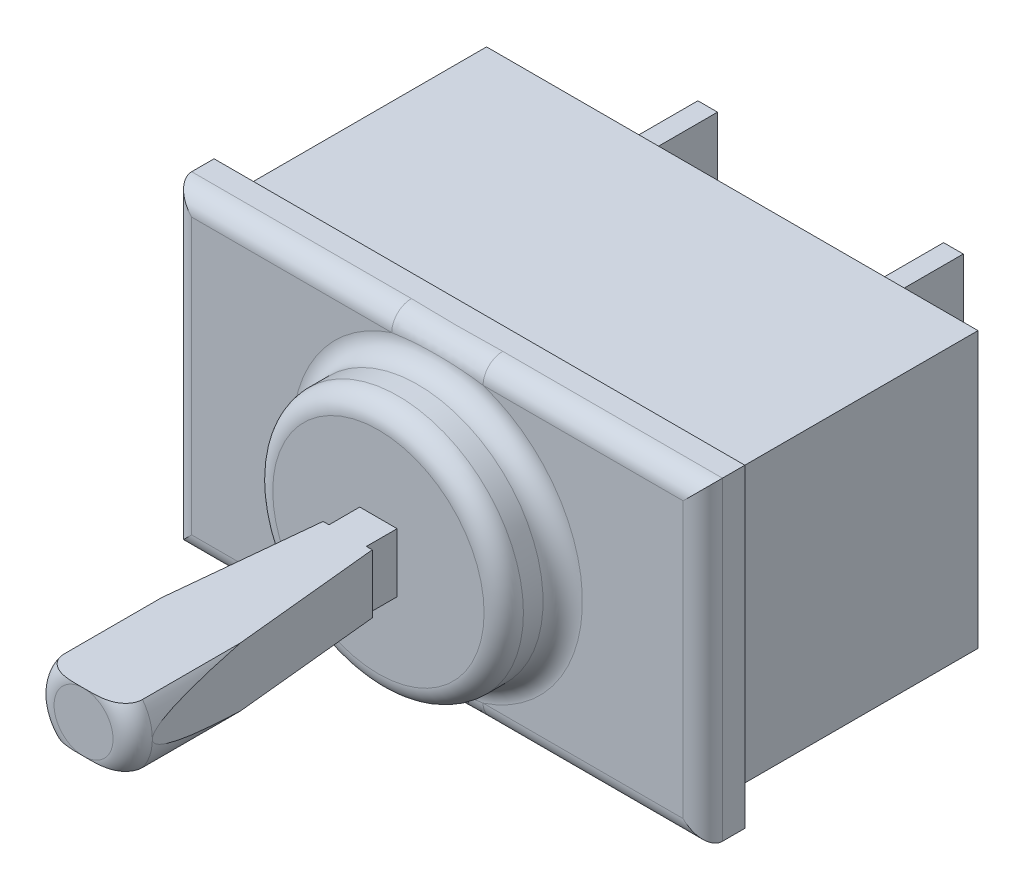
SolidWorks part; units mm, degrees
ref_plane "Front Plane" through (0, 0, 0) normal (0, 0, 1) x (1, 0, 0)
ref_plane "Top Plane" through (0, 0, 0) normal (0, 1, 0) x (1, 0, 0)
ref_plane "Right Plane" through (0, 0, 0) normal (1, 0, 0) x (0, 0, -1)
sketch "Esquisse1" plane through (0, 0, 0) normal (0, 1, 0) x (1, 0, 0)
  line L1 (-13.5, -7.5) -> (13.5, -7.5)
  line L2 (-13.5, -7.5) -> (-13.5, 7.5)
  line L3 (-13.5, 7.5) -> (13.5, 7.5)
  line L4 (13.5, -7.5) -> (13.5, 7.5)
  line L5 (-13.5, -7.5) -> (13.5, 7.5) construction
  line L6 (-13.5, 7.5) -> (13.5, -7.5) construction
  point P0 (0, 0)
  dimension "D1" = 27
  dimension "D2" = 15
extrude "Boss.-Extru.1" add sketch "Esquisse1" along normal blind 16
sketch "Esquisse2" plane through (0, 0, 0) normal (0, -1, 0) x (1, 0, 0)
  line L0 (-13.5, -7.5) -> (-13.5, 7.5) construction
  line L1 (-13.5, 5.3607) -> (13.5, 5.3607)
  line L2 (-13.5, 5.3607) -> (-13.5, -7.5)
  line L3 (-13.5, -7.5) -> (13.5, -7.5)
  line L4 (13.5, 5.3607) -> (13.5, -7.5)
  line L6 (-12.5, 5.3607) -> (12.5, 5.3607)
  line L7 (-12.5, 5.3607) -> (-12.5, -7.5)
  line L8 (-12.5, -7.5) -> (12.5, -7.5)
  line L9 (12.5, 5.3607) -> (12.5, -7.5)
  line M5 (13.5, -7.5) -> (13.5, 7.5)
  line M7 (-13.5, 7.5) -> (-13.5, -7.5)
  line M8 (-13.5, -7.5) -> (13.5, -7.5)
  dimension "D1" = 1
  dimension "D2" = 1
extrude "Enlèv. mat.-Extru.1" cut sketch "Esquisse2" against normal blind 16 contours L7 L1 M7 M8 | L1 L9 M8 M5
sketch "Esquisse3" plane through (12.5, 0, 0) normal (1, 0, 0) x (0, 0, -1)
  line L0 (7.5, 16) -> (7.5, 0) construction
  line L1 (-5.3607, 0) -> (7.5, 0)
  line L2 (-5.3607, 0) -> (-5.3607, 1)
  line L3 (-5.3607, 1) -> (7.5, 1)
  line L4 (7.5, 0) -> (7.5, 1)
  line L6 (-5.3607, 16) -> (7.5, 16)
  line L7 (-5.3607, 16) -> (-5.3607, 15)
  line L8 (-5.3607, 15) -> (7.5, 15)
  line L9 (7.5, 16) -> (7.5, 15)
  dimension "D1" = 1
  dimension "D2" = 1
extrude "Enlèv. mat.-Extru.2" cut sketch "Esquisse3" against normal blind 26
sketch "Esquisse4" plane through (0, 0, 7.5) normal (0, 0, 1) x (1, 0, 0)
  line L0 (0, 0) -> (0, 16) construction
  line L1 (-13.5, 16) -> (13.5, 16) construction
  circle A0 centre (0, 8) radius 6.3756
extrude "Boss.-Extru.2" add sketch "Esquisse4" along normal blind 3
sketch "Esquisse5" plane through (0, 0, 10.5) normal (0, 0, 1) x (1, 0, 0)
  line L0 (0, 1.6244) -> (0, 14.3756) construction
  circle A0 centre (0, 8) radius 6.3756 construction
  circle A1 centre (0, 8) radius 6.3756 construction
  circle A2 centre (0, 8) radius 2.5
  dimension "D1" = 5
extrude "Boss.-Extru.3" add sketch "Esquisse5" along normal blind 15
fillet "Congé4" radius 1 1 edges at (2.5, 8, 25.5)
sketch "Esquisse6" plane through (0, 16, 0) normal (0, 1, 0) x (1, 0, 0)
  line L0 (0, -5.3607) -> (0, -26.7161) construction
  line L1 (-13.5, -5.3607) -> (13.5, -5.3607) construction
  line L2 (-6.3756, -10.5) -> (6.3756, -10.5) construction
  line L3 (3.759, -10.5) -> (-3.759, -10.5)
  line L4 (3.759, -10.5) -> (3.759, -25.9537)
  line L5 (3.759, -25.9537) -> (-3.759, -25.9537)
  line L6 (-3.759, -10.5) -> (-3.759, -25.9537)
  line L7 (3.759, -10.5) -> (-3.759, -25.9537) construction
  line L8 (3.759, -25.9537) -> (-3.759, -10.5) construction
  point P5 (0, -18.2269)
  dimension "D1" = 0
extrude "Enlèv. mat.-Extru.4" cut sketch "Esquisse6" against normal blind 6.5
sketch "Esquisse7" plane through (0, 0, 0) normal (0, -1, 0) x (1, 0, 0)
  line L0 (0, 5.3607) -> (0, 26.7157) construction
  line L1 (-13.5, 5.3607) -> (13.5, 5.3607) construction
  line L2 (6.3756, 10.5) -> (-6.3756, 10.5) construction
  line L3 (-3.6345, 10.5) -> (3.6345, 10.5)
  line L4 (-3.6345, 10.5) -> (-3.6345, 25.5973)
  line L5 (-3.6345, 25.5973) -> (3.6345, 25.5973)
  line L6 (3.6345, 10.5) -> (3.6345, 25.5973)
  line L7 (-3.6345, 10.5) -> (3.6345, 25.5973) construction
  line L8 (-3.6345, 25.5973) -> (3.6345, 10.5) construction
  point P5 (0, 18.0487)
  dimension "D1" = 0
extrude "Enlèv. mat.-Extru.5" cut sketch "Esquisse7" against normal blind 6.5
sketch "Esquisse8" plane through (0, 9.5, 0) normal (0, 1, 0) x (1, 0, 0)
  line L0 (0, -10.5) -> (0, -25.5) construction
  line L1 (2, -10.5) -> (-2, -10.5) construction
  line L2 (2.5, -10.5) -> (-2.5, -10.5)
  line L3 (-2.5, -10.5) -> (-2.5, -24.5)
  line L4 (-2.5, -24.5) -> (-1.25, -12.064)
  line L5 (-2.5, -10.5) -> (-0.9512, -10.5)
  line L6 (-0.9512, -10.5) -> (-0.9512, -12.064)
  line L7 (-0.9512, -12.064) -> (-1.25, -12.064)
  line L8 (2.5, -24.5) -> (1.25, -12.064)
  line L9 (2.5, -10.5) -> (2.5, -24.5)
  line L10 (0.9512, -10.5) -> (0.9512, -12.064)
  line L11 (0.9512, -12.064) -> (1.25, -12.064)
  line M14 (2, -24.5) -> (2, -10.5)
  line M15 (2, -10.5) -> (-2, -10.5)
extrude "Enlèv. mat.-Extru.6" cut sketch "Esquisse8" against normal blind 6.5 contours L10 L11 L8 M14 M15 | L9 L2 L8 M14 | L5 L6 L7 L4 L3
fillet "Congé5" radius 1 2 edges at (6.3756, 8, 7.5) (6.3756, 8, 10.5)
fillet "Congé6" radius 1 4 edges at (-13.5, 8, 7.5) (0, 0, 7.5) (13.5, 8, 7.5) (0, 16, 7.5)
sketch "Esquisse9" plane through (0, 0, -7.5) normal (0, 0, -1) x (-1, 0, 0)
  line L0 (12.5, 8) -> (-12.5, 8) construction
  line L1 (12.5, 15) -> (12.5, 1) construction
  line L2 (-12.5, 15) -> (-12.5, 1) construction
  line L3 (-12.5, 8) -> (0, 8) construction
  line L4 (0, 8) -> (12.5, 8) construction
  line L5 (0, 8) -> (-12.5, 8) construction
  line L6 (5.75, 13) -> (6.75, 13)
  line L7 (5.75, 13) -> (5.75, 3)
  line L8 (5.75, 3) -> (6.75, 3)
  line L9 (6.75, 13) -> (6.75, 3)
  line L10 (5.75, 13) -> (6.75, 3) construction
  line L11 (5.75, 3) -> (6.75, 13) construction
  line L13 (-6.75, 13) -> (-5.75, 13)
  line L14 (-6.75, 13) -> (-6.75, 3)
  line L15 (-6.75, 3) -> (-5.75, 3)
  line L16 (-5.75, 13) -> (-5.75, 3)
  line L17 (-6.75, 13) -> (-5.75, 3) construction
  line L18 (-6.75, 3) -> (-5.75, 13) construction
  point P6 (6.25, 8)
  point P12 (-6.25, 8)
  dimension "D1" = 1
  dimension "D2" = 1
  dimension "D3" = 10
  dimension "D4" = 10
extrude "Boss.-Extru.4" add sketch "Esquisse9" along normal blind 5
sketch "Esquisse10" plane through (-6.75, 0, 0) normal (-1, 0, 0) x (0, 0, 1)
  line L0 (-10, 13) -> (-10, 3) construction
  line L1 (-12.5, 13) -> (-7.5, 13) construction
  line L2 (-12.5, 3) -> (-7.5, 3) construction
  circle A0 centre (-10, 8) radius 1.625
  dimension "D1" = 3.25
extrude "Enlèv. mat.-Extru.7" cut sketch "Esquisse10" against normal blind 18
